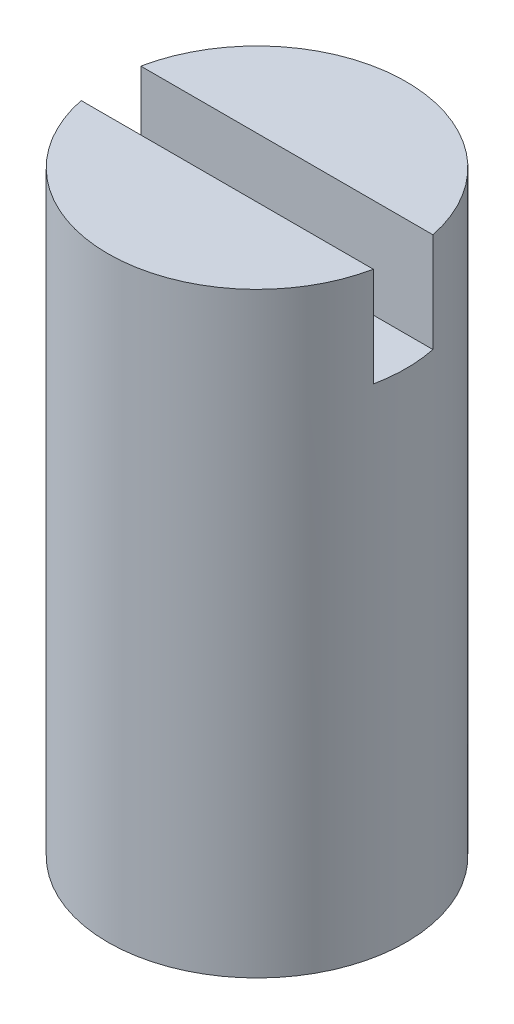
SolidWorks part; units mm, degrees
material "6061-T6 (SS)"
ref_plane "X-Y Datum" through (0, 0, 0) normal (0, 0, 1) x (1, 0, 0)
ref_plane "X-Z Datum" through (0, 0, 0) normal (0, 1, 0) x (1, 0, 0)
ref_plane "Y-Z Datum" through (0, 0, 0) normal (1, 0, 0) x (0, 0, -1)
sketch "Sketch1" plane through (0, 0, 0) normal (0, 1, 0) x (1, 0, 0)
  circle A0 centre (0, 0) radius 4.7625
  dimension "D1" = 9.525
extrude "Boss-Extrude1" add sketch "Sketch1" against normal blind 19.05
sketch "Sketch2" plane through (0, 0, 0) normal (0, 1, 0) x (1, 0, 0)
  line L5 (4.7625, 0.9525) -> (-4.7625, 0.9525)
  line L6 (4.7625, 0.9525) -> (4.7625, -0.9525)
  line L7 (4.7625, -0.9525) -> (-4.7625, -0.9525)
  line L8 (-4.7625, 0.9525) -> (-4.7625, -0.9525)
  line L9 (4.7625, 0.9525) -> (-4.7625, -0.9525) construction
  line L10 (4.7625, -0.9525) -> (-4.7625, 0.9525) construction
  point P0 (0, 0)
  dimension "D1" = 9.525
  dimension "D2" = 1.905
extrude "Cut-Extrude1" cut sketch "Sketch2" against normal blind 3.175
sketch "Sketch3" plane through (0, -19.05, 0) normal (0, -1, 0) x (1, 0, 0)
  circle A0 centre (0, 0) radius 2
  dimension "D1" = 4
extrude "Cut-Extrude2" cut sketch "Sketch3" against normal blind 8
